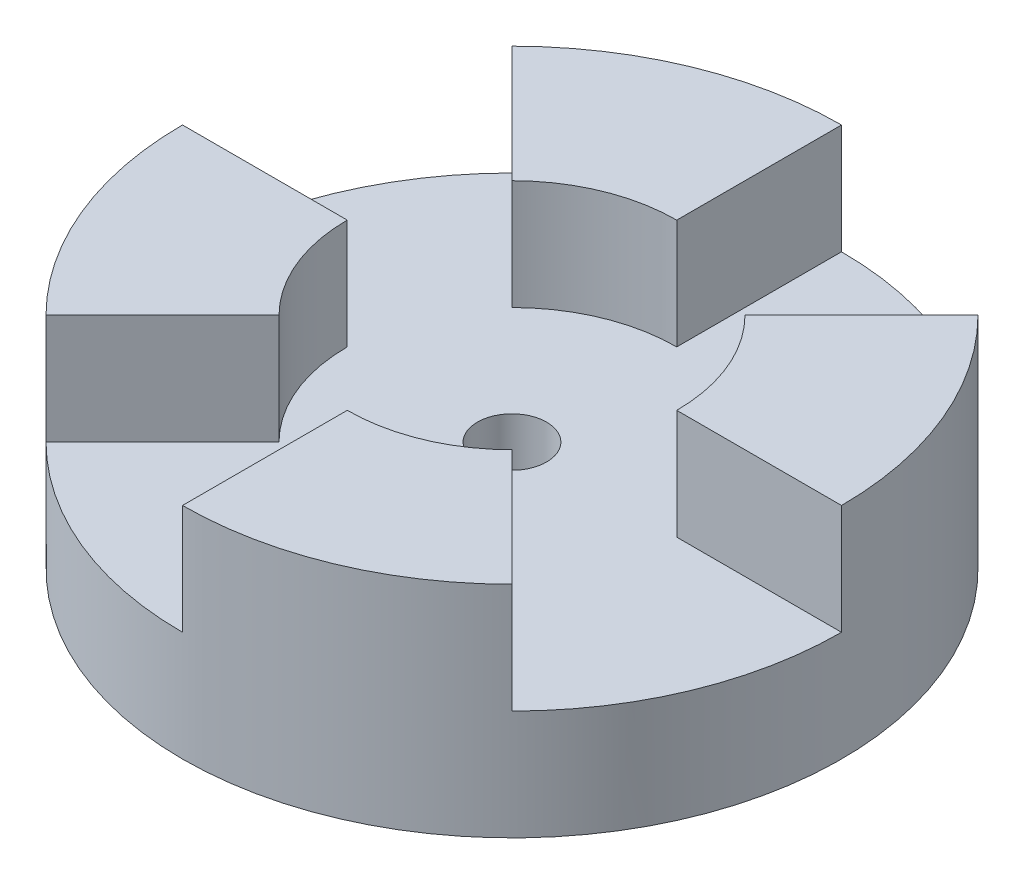
SolidWorks part; units mm, degrees
ref_plane "Front Plane" through (0, 0, 0) normal (0, 0, 1) x (1, 0, 0)
ref_plane "Top Plane" through (0, 0, 0) normal (0, 1, 0) x (1, 0, 0)
ref_plane "Right Plane" through (0, 0, 0) normal (1, 0, 0) x (0, 0, -1)
sketch "Sketch1" plane through (0, 0, 0) normal (0, 1, 0) x (1, 0, 0)
  circle A0 centre (-80.7899, -8.4156) radius 38.1
extrude "Boss-Extrude1" add sketch "Sketch1" along normal blind 12.7
sketch "Sketch2" plane through (0, 12.7, 0) normal (0, 1, 0) x (1, 0, 0)
  circle A0 centre (-80.7899, -8.4156) radius 4.0005
extrude "Cut-Extrude1" cut sketch "Sketch2" against normal blind 12.7
sketch "Sketch3" plane through (0, 12.7, 0) normal (0, 1, 0) x (1, 0, 0)
  line L0 (-67.3195, 5.0548) -> (-53.8491, 18.5252)
  line L1 (-94.2602, 5.0548) -> (-107.7306, 18.5252)
  line L2 (-94.2602, -21.886) -> (-107.7306, -35.3564)
  line L3 (-67.3195, -21.886) -> (-53.8491, -35.3564)
  line L4 (-99.8399, -8.4156) -> (-118.8899, -8.4156)
  line L5 (-80.7899, 10.6344) -> (-80.7899, 29.6844)
  line L6 (-61.7399, -8.4156) -> (-42.6899, -8.4156)
  line L7 (-80.7899, -27.4656) -> (-80.7899, -46.5156)
  arc A1 (-80.7899, 10.6344) -> (-61.7399, -8.4156) centre (-80.7899, -8.4156) cw
  arc A2 (-80.7899, 10.6344) -> (-61.7399, -8.4156) centre (-80.7899, -8.4156) cw
  circle A3 centre (-80.7899, -8.4156) radius 38.1 construction
  arc A4 (-80.7899, 10.6344) -> (-99.8399, -8.4156) centre (-80.7899, -8.4156) ccw
  arc A5 (-99.8399, -8.4156) -> (-80.7899, -27.4656) centre (-80.7899, -8.4156) ccw
  arc A6 (-80.7899, -27.4656) -> (-61.7399, -8.4156) centre (-80.7899, -8.4156) ccw
  circle M2 centre (-80.7899, -8.4156) radius 38.1
extrude "Boss-Extrude2" add sketch "Sketch3" along normal blind 12.7 contours A4 L5 L1 M2 | L0 A1 L6 M2 | A6 L7 L3 M2 | A5 L4 L2 M2
sketch "Sketch5" plane through (0, 0, 0) normal (0, -1, 0) x (1, 0, 0)
  circle A0 centre (-80.7899, 8.4156) radius 5.334
extrude "Cut-Extrude2" cut sketch "Sketch5" against normal blind 2.54
